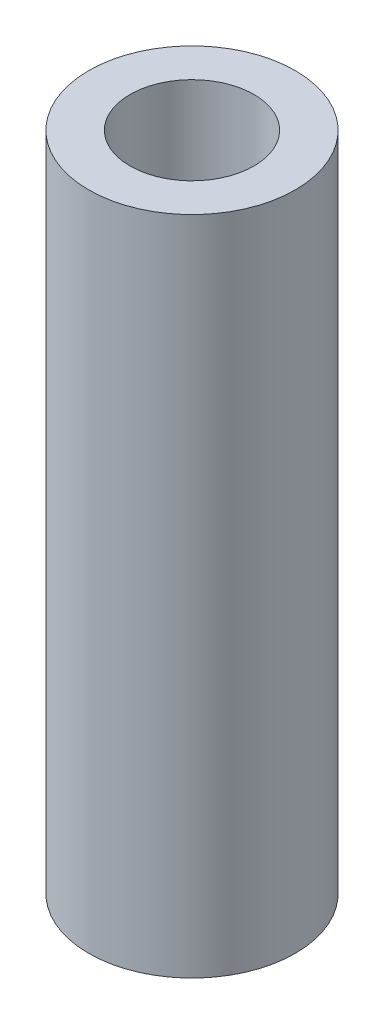
SolidWorks part; units mm, degrees
ref_plane "前视基准面" through (0, 0, 0) normal (0, 0, 1) x (1, 0, 0)
ref_plane "上视基准面" through (0, 0, 0) normal (0, 1, 0) x (1, 0, 0)
ref_plane "右视基准面" through (0, 0, 0) normal (1, 0, 0) x (0, 0, -1)
other "Configuration Table"
sketch "草图1" plane through (0, 0, 0) normal (0, 1, 0) x (1, 0, 0)
  circle A0 centre (0, 0) radius 1.5
  circle A1 centre (0, 0) radius 2.5
  dimension "D1" = 3
  dimension "D2" = 5
extrude "凸台-拉伸1" add sketch "草图1" along normal blind 16
